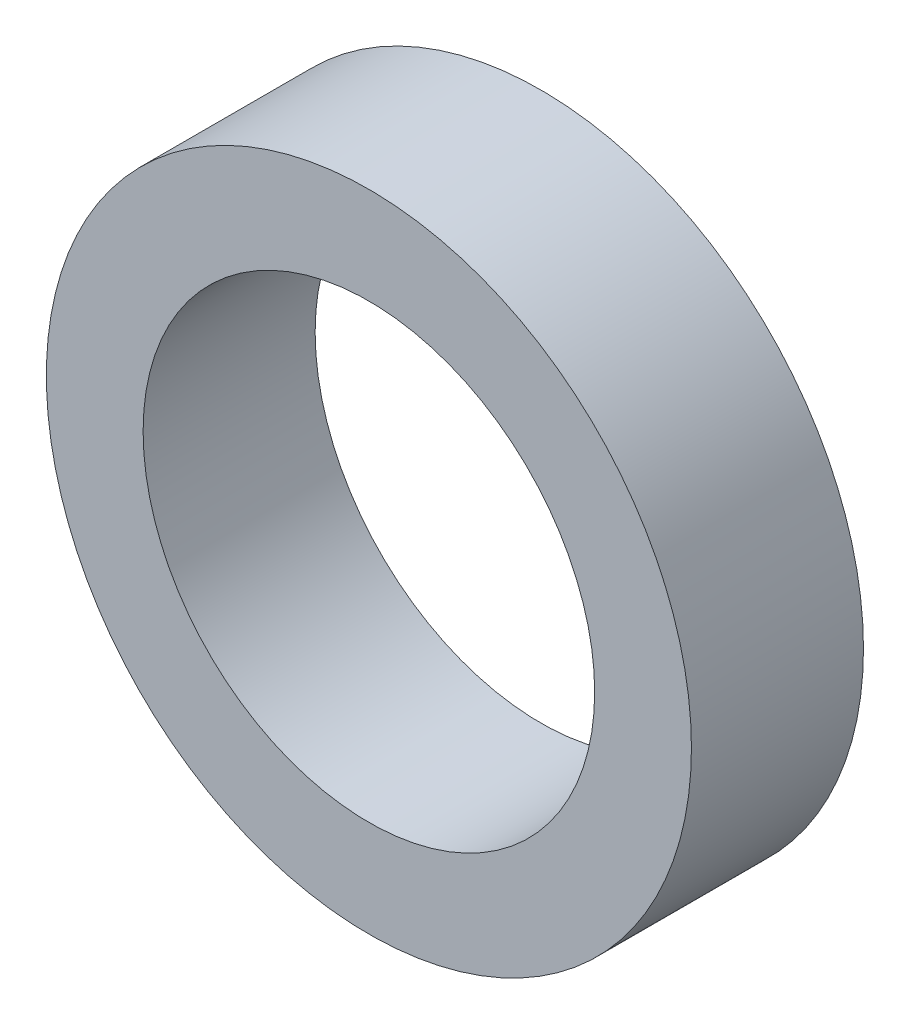
SolidWorks part; units mm, degrees
ref_plane "前视基准面" through (0, 0, 0) normal (0, 0, 1) x (1, 0, 0)
ref_plane "上视基准面" through (0, 0, 0) normal (0, 1, 0) x (1, 0, 0)
ref_plane "右视基准面" through (0, 0, 0) normal (1, 0, 0) x (0, 0, -1)
sketch "草图1" plane through (0, 0, 0) normal (0, 0, 1) x (1, 0, 0)
  circle A0 centre (0, 0) radius 2.1
  circle A1 centre (0, 0) radius 3
extrude "凸台-拉伸1" add sketch "草图1" along normal blind 1.6
